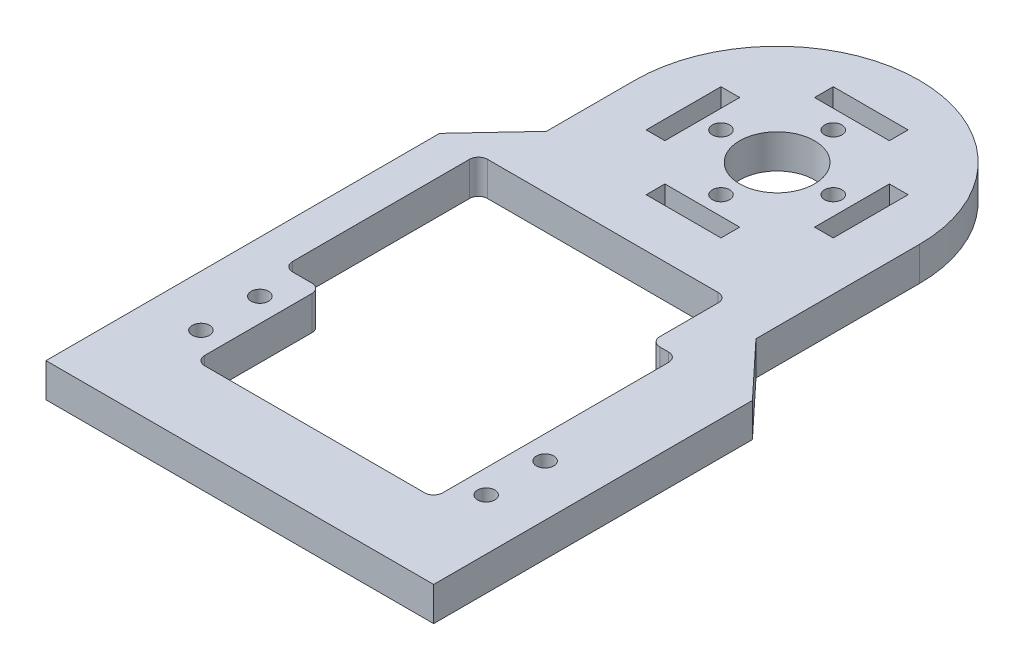
SolidWorks part; units mm, degrees
ref_plane "Front Plane" through (0, 0, 0) normal (0, 0, 1) x (1, 0, 0)
ref_plane "Top Plane" through (0, 0, 0) normal (0, 1, 0) x (1, 0, 0)
ref_plane "Right Plane" through (0, 0, 0) normal (1, 0, 0) x (0, 0, -1)
sketch "Sketch2" plane through (0, 0, 0) normal (0, 1, 0) x (1, 0, 0)
  circle A0 centre (0, 0) radius 24.13
  circle A1 centre (0, 0) radius 27.305 construction
  circle A2 centre (0, 0) radius 6.35
  dimension "D1" = 48.26
  dimension "D2" = 3.175
  dimension "D3" = 12.7
extrude "Boss-Extrude1" add sketch "Sketch2" along normal blind 5.7658
sketch "Sketch5" plane through (0, 5.7658, 0) normal (0, 1, 0) x (1, 0, 0)
  line L0 (0, 16.6687) -> (0, 8.7312) construction
  line L1 (0, -6.35) -> (0, -24.13) construction
  circle A0 centre (0, 16.6687) radius 0.762
  circle A1 centre (0, 8.7312) radius 0.762
  circle A2 centre (0, 12.7) radius 1.9812
  circle A3 centre (0, 0) radius 12.7 construction
  circle A4 centre (0, 0) radius 6.35 construction
  circle A5 centre (0, 0) radius 24.13 construction
  point P0 (0, 16.6687)
  point P1 (0, 8.7312)
  point P2 (0, 12.7)
  dimension "D2" = 1.524
  dimension "D3" = 3.9624
  dimension "D4" = 25.4
  dimension "D1" = 7.9375
hole_wizard "1/16 (0.0625) Press Dowel Hole1" [suppressed] positions "Sketch7" profile "Sketch6" hole size "1/16" standard "ANSI Inch"
sketch "Sketch7" plane through (0, 3.175, 0) normal (0, 1, 0) x (1, 0, 0)
  point P0 (0, 16.6687)
  point P3 (0, 8.7312)
sketch "Sketch6" plane through (0, 3.175, -16.6687) normal (1, 0, 0) x (0, 0, 1)
  line L0 (0, 0) -> (0, 3.176)
  line L1 (0, 3.176) -> (0.762, 3.176)
  line L2 (0.762, 3.176) -> (0.762, 0)
  line L5 (0.762, 0) -> (0, 0)
  line L11 (0, -6.35) -> (0, 107.95) construction
  dimension "Thru Hole Dia." = 1.524
  dimension "Thru Hole Depth" = 3.176
hole_wizard "#4 Clearance Hole1" [suppressed] positions "Sketch9" profile "Sketch8" hole size "#4" standard "ANSI Inch"
sketch "Sketch9" plane through (0, 3.175, 0) normal (0, 1, 0) x (1, 0, 0)
  point P0 (0, 12.7)
sketch "Sketch8" plane through (0, 3.175, -12.7) normal (1, 0, 0) x (0, 0, 1)
  line L0 (0, 0) -> (0, 3.175)
  line L1 (0, 3.175) -> (1.4732, 3.175)
  line L2 (1.4732, 3.175) -> (1.4732, 0)
  line L5 (1.4732, 0) -> (0, 0)
  line L11 (0, -6.35) -> (0, 107.95) construction
  dimension "Thru Hole Dia." = 2.9464
  dimension "Thru Hole Depth" = 3.175
sketch "Sketch13" plane through (0, 5.7658, 0) normal (0, 1, 0) x (1, 0, 0)
  line L0 (0, 6.35) -> (0, 24.13) construction
  line L1 (3.175, 13.4069) -> (3.175, 17.0731)
  line L2 (3.175, 17.0731) -> (0, 18.9062)
  line L3 (0, 18.9062) -> (-3.175, 17.0731)
  line L4 (-3.175, 17.0731) -> (-3.175, 13.4069)
  line L5 (-3.175, 13.4069) -> (0, 11.5738)
  line L6 (0, 11.5738) -> (3.175, 13.4069)
  circle A0 centre (0, 15.24) radius 3.175 construction
  circle A1 centre (0, 0) radius 6.35 construction
  circle A2 centre (0, 0) radius 24.13 construction
  dimension "D1" = 6.35
extrude "Cut-Extrude3" [suppressed] cut sketch "Sketch13" against normal up to next contours L3 L4 L5 L6 L1 L2
sketch "Sketch10" plane through (0, 5.7658, 0) normal (0, 1, 0) x (1, 0, 0)
  line L0 (0, 0) -> (0, 24.13) construction
  line L1 (-3.1279, 0) -> (4.3423, 0) construction
  line L2 (-6.35, 15.875) -> (6.35, 15.875)
  line L3 (-6.35, 15.875) -> (-6.35, 12.7)
  line L4 (-6.35, 12.7) -> (6.35, 12.7)
  line L5 (6.35, 15.875) -> (6.35, 12.7)
  line L6 (-6.35, 15.875) -> (6.35, 12.7) construction
  line L7 (-6.35, 12.7) -> (6.35, 15.875) construction
  circle A0 centre (0, 0) radius 24.13 construction
  point P0 (0, 14.2875)
  dimension "D1" = 3.175
  dimension "D2" = 25.4
  dimension "D3" = 12.7
extrude "Cut-Extrude2" cut sketch "Sketch10" against normal up to next (5.7658 mm away)
hole_wizard "#4 Clearance Hole2" positions "Sketch15" profile "Sketch14" hole size "#4" standard "ANSI Inch" end condition up to next
sketch "Sketch15" plane through (0, 5.7658, 0) normal (0, 1, 0) x (1, 0, 0)
  line L0 (0, 6.35) -> (0, 24.13) construction
  circle A0 centre (0, 0) radius 6.35 construction
  circle A1 centre (0, 0) radius 24.13 construction
  point P0 (0, 9.525)
  dimension "D1" = 9.525
sketch "Sketch14" plane through (0, 5.7658, -9.525) normal (1, 0, 0) x (0, 0, 1)
  line L0 (0, 0) -> (0, 5.7668)
  line L1 (0, 5.7668) -> (1.4732, 5.7668)
  line L2 (1.4732, 5.7668) -> (1.4732, 0)
  line L5 (1.4732, 0) -> (0, 0)
  line L11 (0, -6.35) -> (0, 107.95) construction
  dimension "Thru Hole Dia." = 2.9464
  dimension "Thru Hole Depth" = 5.7668
pattern_circular "CirPattern2" count 4 over 360 about axis through (0, 0, 0) along (0, 1, 0) of "Cut-Extrude2", "#4 Clearance Hole2"
sketch "Sketch16" plane through (0, 5.7658, 0) normal (0, 1, 0) x (1, 0, 0)
  line L0 (-24.13, 0) -> (-24.13, -27.7215)
  line L1 (-32.893, -37.084) -> (-24.13, -27.7215)
  line L2 (-32.893, -91.174) -> (32.893, -91.174)
  line L4 (-15.6591, -37.084) -> (-20.193, -37.084)
  line L5 (-15.6591, -18.3589) -> (-15.6591, -37.084)
  line L6 (-24.2, -68.574) -> (24.2, -68.574) construction
  line L7 (15.6591, -18.3589) -> (15.6591, -37.084)
  line L8 (-15.6591, -18.3589) -> (15.6591, -37.084) construction
  line L9 (-15.6591, -37.084) -> (15.6591, -18.3589) construction
  line L10 (-20.193, -58.674) -> (-20.193, -78.474)
  line L11 (-20.193, -78.474) -> (20.193, -78.474)
  line L12 (20.193, -58.674) -> (20.193, -78.474)
  line L13 (0, -27.7215) -> (0, -68.574) construction
  line L14 (32.893, -37.084) -> (32.893, -91.174)
  line L15 (-32.893, -37.084) -> (-32.893, -91.174)
  line L16 (32.893, -37.084) -> (24.13, -27.7215)
  line L17 (24.13, -27.7215) -> (24.13, 0)
  line L18 (-24.2, -63.574) -> (-24.2, -73.574) construction
  line L19 (15.6591, -37.084) -> (20.193, -37.084)
  line L20 (20.193, -37.084) -> (20.193, -58.674)
  line L21 (-20.193, -37.084) -> (-20.193, -58.674)
  circle A0 centre (0, 0) radius 24.13 construction
  arc A1 (-24.13, 0) -> (-15.6591, -18.3589) centre (0, 0) ccw
  arc A2 (15.6591, -18.3589) -> (24.13, 0) centre (0, 0) ccw
  circle A3 centre (-24.2, -63.574) radius 1.7018 construction
  circle A4 centre (-24.2, -73.574) radius 1.7018 construction
  circle A5 centre (24.2, -73.574) radius 1.7018 construction
  circle A6 centre (24.2, -63.574) radius 1.7018 construction
  point P6 (0, -27.7215)
  point P16 (0, -78.474)
  point P27 (-20.193, -68.574)
  dimension "D7" = 3.4036
  dimension "D1" = 31.3182
  dimension "D2" = 68.574
  dimension "D3" = 21.59
  dimension "D4" = 40.386
  dimension "D5" = 48.4
  dimension "D6" = 10
  dimension "D8" = 12.7
  dimension "D9" = 19.8
  dimension "D10" = 12.7
extrude "Boss-Extrude2" add sketch "Sketch16" against normal up to surface (5.7658 mm away) up to face at (-9.525, 0, 1.4732)
sketch "Sketch32" plane through (0, 5.7658, 0) normal (0, 1, 0) x (1, 0, 0)
  line L0 (-15.6591, -24.13) -> (15.6591, -24.13)
  line L1 (-15.6591, -37.084) -> (-15.6591, -18.3589) construction
  line L2 (15.6591, -18.3589) -> (15.6591, -37.084) construction
  line L3 (-15.6591, -18.3589) -> (-15.6591, -24.13)
  line L4 (15.6591, -18.3589) -> (15.6591, -24.13)
  arc A0 (-15.6591, -18.3589) -> (15.6591, -18.3589) centre (0, 0) ccw construction
  arc A1 (-15.6591, -18.3589) -> (15.6591, -18.3589) centre (0, 0) ccw
  arc M29 (-15.6591, -18.3589) -> (15.6591, -18.3589) centre (0, 0) ccw
  line M30 (15.6591, -18.3589) -> (15.6591, -37.084)
  line M36 (-15.6591, -37.084) -> (-15.6591, -18.3589)
extrude "Boss-Extrude4" add sketch "Sketch32" against normal up to surface (5.7658 mm away) contours L0 M29 M30 | L0 M36 M29 up to face at (0, 0, 35.9786)
hole_wizard "#4 Clearance Hole3" positions "Sketch29" profile "Sketch28" hole size "#4" standard "ANSI Inch" end condition up to next
sketch "Sketch29" plane through (0, 5.7658, 0) normal (0, 1, 0) x (1, 0, 0)
  point P0 (-24.2, -63.574)
  point P3 (-24.2, -73.574)
  point P6 (24.2, -63.574)
  point P9 (24.2, -73.574)
sketch "Sketch28" plane through (-24.2, 5.7658, 63.574) normal (1, 0, 0) x (0, 0, 1)
  line L0 (0, 0) -> (0, 5.7658)
  line L1 (0, 5.7658) -> (1.4732, 5.7658)
  line L2 (1.4732, 5.7658) -> (1.4732, 0)
  line L5 (1.4732, 0) -> (0, 0)
  line L11 (0, -6.35) -> (0, 107.95) construction
  dimension "Thru Hole Dia." = 2.9464
  dimension "Thru Hole Depth" = 5.7658
sketch "Sketch31" plane through (0, 5.7658, 0) normal (0, 1, 0) x (1, 0, 0)
  line L0 (-32.893, -37.084) -> (-32.893, -24.384)
  line L2 (-24.13, 0) -> (-24.13, -27.7215) construction
  line L3 (-24.13, -15.0215) -> (-24.13, -27.7215)
  line L4 (-24.13, -27.7215) -> (-32.893, -37.084)
  line L5 (-32.893, -24.384) -> (-24.13, -15.0215)
  dimension "D1" = 12.7
extrude "Boss-Extrude3" add sketch "Sketch31" against normal up to surface (5.7658 mm away) up to face at (-24.2, 0, 65.0472)
sketch "Sketch30" plane through (0, 5.7658, 0) normal (0, 1, 0) x (1, 0, 0)
  line L0 (-26.543, -17.3427) -> (-26.543, -106.8368) construction
  line L1 (-32.893, -24.384) -> (-32.893, -91.174) construction
  line L2 (-26.543, -57.224) -> (-15.6591, -57.224)
  line L4 (-26.543, -57.224) -> (-26.543, -24.13)
  line L5 (-26.543, -24.13) -> (-15.6591, -24.13)
  line L6 (-15.6591, -24.13) -> (-15.6591, -57.224)
  line L7 (-15.6591, -24.13) -> (15.6591, -24.13) construction
  line L9 (-15.6591, -37.084) -> (-15.6591, -24.13) construction
  circle A0 centre (-24.2, -63.574) radius 1.4732 construction
  dimension "D1" = 6.35
  dimension "D2" = 6.35
extrude "Cut-Extrude4" cut sketch "Sketch30" against normal up to next
fillet "Fillet2" radius 1.524 8 edges at (-20.193, 2.8829, 78.474) (20.193, 2.8829, 78.474) (20.193, 2.8829, 37.084) (-26.543, 2.8829, 57.224) (-26.543, 2.8829, 24.13) (15.6591, 2.8829, 37.084) (-20.193, 2.8829, 57.224) (15.6591, 2.8829, 24.13)
